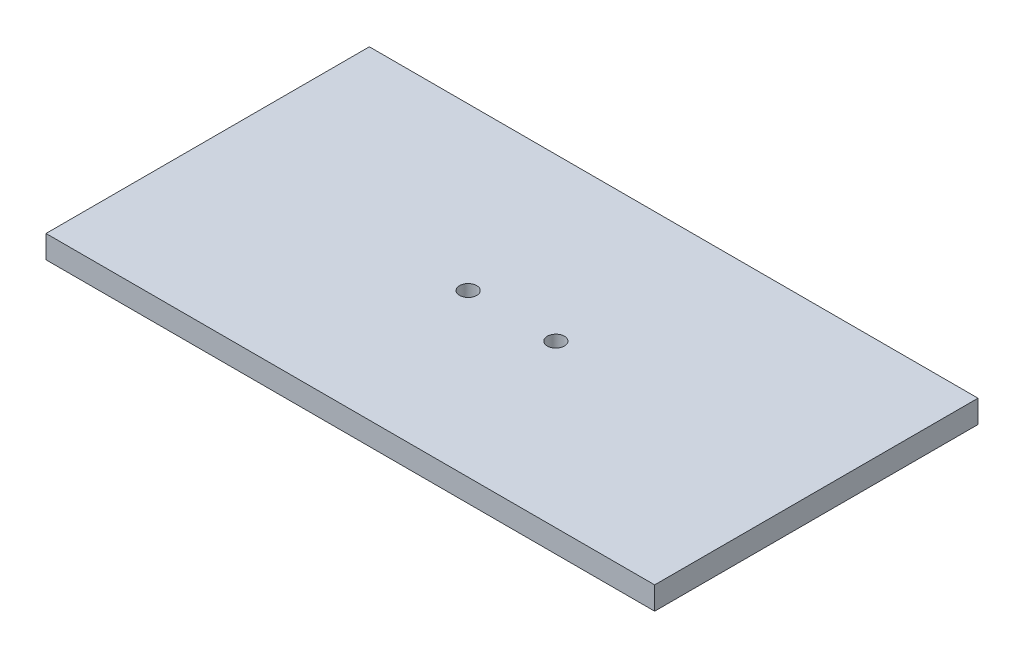
SolidWorks part; units mm, degrees
ref_plane "Plano frontal" through (0, 0, 0) normal (0, 0, 1) x (1, 0, 0)
ref_plane "Plano superior" through (0, 0, 0) normal (0, 1, 0) x (1, 0, 0)
ref_plane "Plano direito" through (0, 0, 0) normal (1, 0, 0) x (0, 0, -1)
sketch "Esboço1" plane through (0, 0, 0) normal (0, 1, 0) x (1, 0, 0)
  line L1 (-160, -85) -> (160, -85)
  line L2 (-160, -85) -> (-160, 85)
  line L3 (-160, 85) -> (160, 85)
  line L4 (160, -85) -> (160, 85)
  line L5 (-160, -85) -> (160, 85) construction
  line L6 (-160, 85) -> (160, -85) construction
  point P0 (0, 0)
  dimension "D1" = 320
  dimension "D2" = 170
extrude "Ressalto-extrusão1" add sketch "Esboço1" along normal blind 12
sketch "Esboço2" plane through (0, 12, 0) normal (0, 1, 0) x (1, 0, 0)
  circle A0 centre (-23.05, 0) radius 4.5
  circle A1 centre (23.05, 0) radius 4.5
  dimension "D1" = 9
  dimension "D2" = 9
  dimension "D3" = 46.1
  dimension "D4" = 23.05
extrude "Corte-extrusão1" cut sketch "Esboço2" against normal through all both and the other way through all
equation "\"D4@Esboço2\"=\"D3@Esboço2\"/2"
